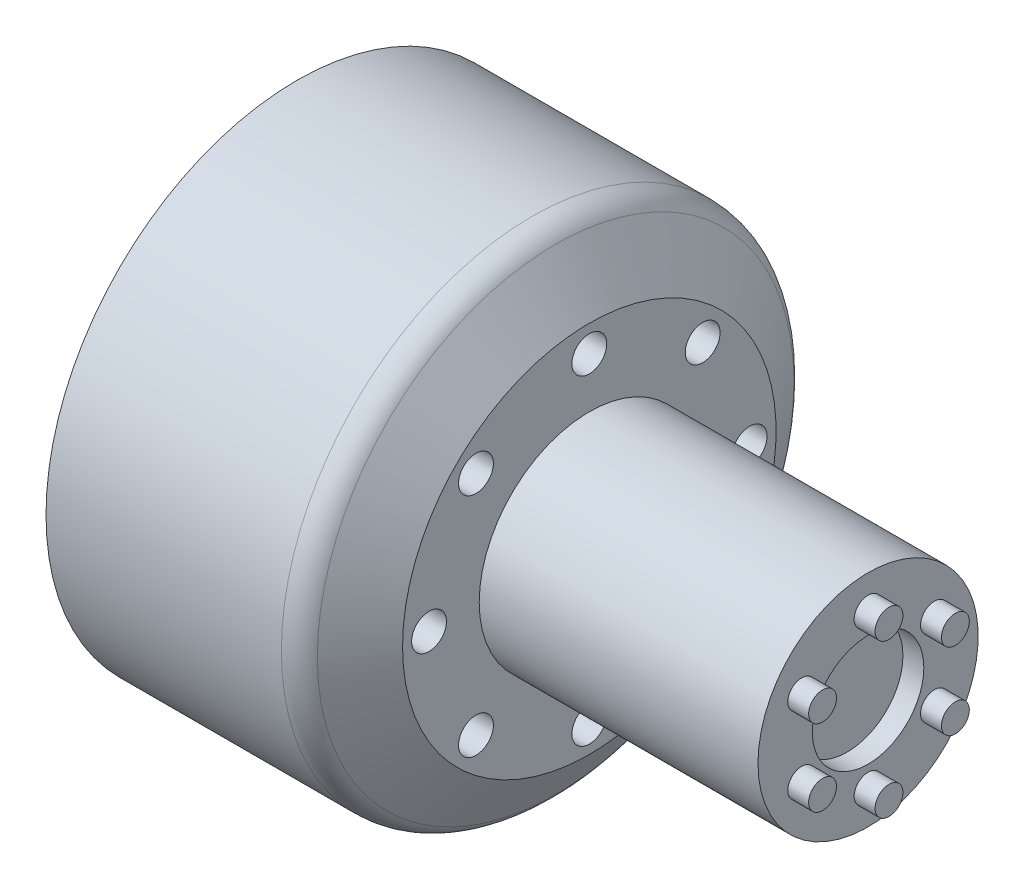
SolidWorks part; units mm, degrees
ref_plane "Front Plane" through (0, 0, 0) normal (0, 0, 1) x (1, 0, 0)
ref_plane "Top Plane" through (0, 0, 0) normal (0, 1, 0) x (1, 0, 0)
ref_plane "Right Plane" through (0, 0, 0) normal (1, 0, 0) x (0, 0, -1)
sketch "Sketch1" plane through (0, 0, 0) normal (0, 1, 0) x (1, 0, 0)
  line L0 (-26.116, 0) -> (40.4037, 0) construction
  line L1 (7.1438, 7.9) -> (7.1438, 13.4)
  line L2 (7.1438, 13.4) -> (4.1337, 18)
  line L3 (4.1337, 18) -> (-13.8362, 18)
  line L4 (-13.8362, 18) -> (-13.8362, 0)
  line L5 (-13.8362, 0) -> (7.1438, 0)
  line L6 (7.1438, 7.9) -> (27.1438, 7.9)
  line L7 (27.1438, 7.9) -> (27.1438, 0)
  line L8 (7.1438, 0) -> (27.1438, 0)
  dimension "D1" = 20.98
  dimension "D2" = 13.4
  dimension "D3" = 123.2
  dimension "D4" = 18
  dimension "D5" = 15.8
  dimension "D6" = 20
revolve "Revolve1" add sketch "Sketch1" angle 360 about L0
sketch "Sketch2" plane through (7.1438, 0, 0) normal (1, 0, 0) x (0, 0, -1)
  circle A0 centre (0, 0) radius 11.5 construction
  circle A1 centre (0, 11.5) radius 1.25
  circle A2 centre (8.1317, 8.1317) radius 1.25
  circle A3 centre (11.5, 0) radius 1.25
  circle A4 centre (8.1317, -8.1317) radius 1.25
  circle A5 centre (0, -11.5) radius 1.25
  circle A6 centre (-8.1317, -8.1317) radius 1.25
  circle A7 centre (-11.5, 0) radius 1.25
  circle A8 centre (-8.1317, 8.1317) radius 1.25
  point P22 (0, 0)
  dimension "D1" = 23
  dimension "D2" = 2.5
  dimension "D3" = 8
extrude "Cut-Extrude1" cut sketch "Sketch2" against normal through all
sketch "Sketch3" plane through (-13.8362, 0, 0) normal (-1, 0, 0) x (0, 0, 1)
  circle A0 centre (0, 0) radius 11.5 construction
  circle A1 centre (0, 11.5) radius 2.5
  circle A2 centre (8.1317, 8.1317) radius 2.5
  circle A3 centre (11.5, 0) radius 2.5
  circle A4 centre (8.1317, -8.1317) radius 2.5
  circle A5 centre (0, -11.5) radius 2.5
  circle A6 centre (-8.1317, -8.1317) radius 2.5
  circle A7 centre (-11.5, 0) radius 2.5
  circle A8 centre (-8.1317, 8.1317) radius 2.5
  point P22 (0, 0)
  dimension "D1" = 23
  dimension "D2" = 5
  dimension "D3" = 8
extrude "Cut-Extrude2" cut sketch "Sketch3" against normal offset from surface (15.98 mm away) 5 up to face at (7.1438, 11.5, -1.25)
sketch "Sketch4" plane through (-13.8362, 0, 0) normal (-1, 0, 0) x (0, 0, 1)
  circle A0 centre (0, 0) radius 9.5
  dimension "D1" = 19
extrude "Cut-Extrude3" cut sketch "Sketch4" against normal blind 10
fillet "Fillet2" radius 2 1 edges at (4.1337, 0, 18)
sketch "Sketch6" plane through (27.1438, 0, 0) normal (1, 0, 0) x (0, 0, -1)
  circle A0 centre (0, 0) radius 4
  dimension "D1" = 8
extrude "Cut-Extrude5" cut sketch "Sketch6" against normal blind 1.5
sketch "Sketch7" plane through (27.1438, 0, 0) normal (1, 0, 0) x (0, 0, -1)
  circle A0 centre (0, 0) radius 5.5 construction
  circle A1 centre (0, 5.5) radius 1
  circle A2 centre (4.7631, 2.75) radius 1
  circle A3 centre (4.7631, -2.75) radius 1
  circle A4 centre (0, -5.5) radius 1
  circle A5 centre (-4.7631, -2.75) radius 1
  circle A6 centre (-4.7631, 2.75) radius 1
  point P18 (0, 0)
  dimension "D1" = 2
  dimension "D2" = 11
  dimension "D3" = 6
extrude "Boss-Extrude1" add sketch "Sketch7" along normal blind 1.5
